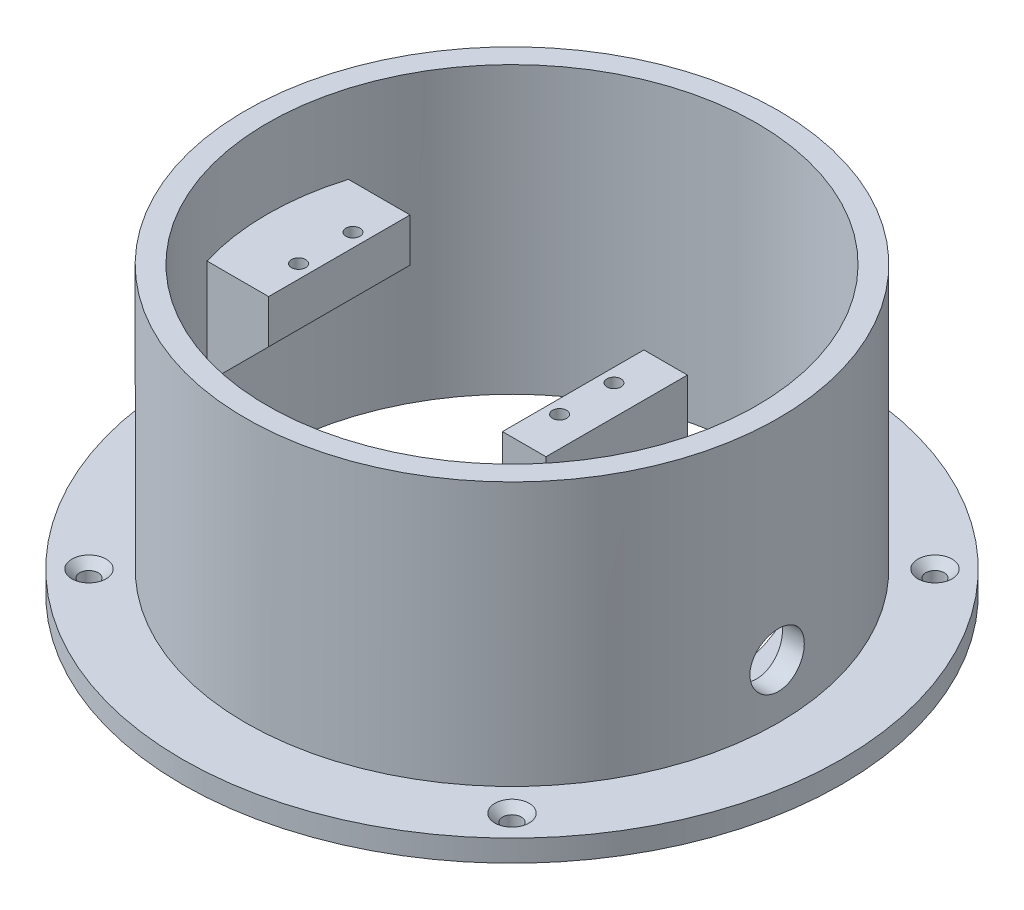
SolidWorks part; units mm, degrees
ref_plane "Front Plane" through (0, 0, 0) normal (0, 0, 1) x (1, 0, 0)
ref_plane "Top Plane" through (0, 0, 0) normal (0, 1, 0) x (1, 0, 0)
ref_plane "Right Plane" through (0, 0, 0) normal (1, 0, 0) x (0, 0, -1)
sketch "Sketch1" plane through (0, 0, 0) normal (0, 1, 0) x (1, 0, 0)
  circle A0 centre (0, 0) radius 60.625
  circle A1 centre (0, 0) radius 45
  dimension "D1" = 121.25
  dimension "D2" = 90
extrude "Boss-Extrude1" add sketch "Sketch1" along normal blind 4 contours A0
sketch "Sketch2" plane through (0, 4, 0) normal (0, 1, 0) x (1, 0, 0)
  circle A0 centre (0, 0) radius 45 construction
  circle A1 centre (0, 0) radius 45
  circle A2 centre (0, 0) radius 49
  dimension "D1" = 4
extrude "Boss-Extrude2" add sketch "Sketch2" along normal blind 52
ref_plane "Plane1" through (0, 36, 0) normal (0, 1, 0) x (1, 0, 0)
sketch "Sketch4" plane through (0, 0, 0) normal (0, 0, 1) x (1, 0, 0)
  line L0 (-60.625, 0) -> (60.625, 0) construction
  line L1 (11.25, 38) -> (19.25, 38)
  line L2 (11.25, 38) -> (11.25, 0)
  line L3 (11.25, 0) -> (19.25, 0)
  line L4 (19.25, 38) -> (19.25, 0)
  line L5 (49, 56) -> (-49, 56) construction
  line L6 (-45, 56) -> (-45, 4)
  line L7 (-31.75, 38) -> (-46.75, 38)
  line L8 (-31.75, 38) -> (-31.75, 30)
  line L9 (-31.75, 30) -> (-46.75, 30)
  line L10 (-46.75, 38) -> (-46.75, 30)
  line L11 (60.625, 4) -> (-60.625, 4) construction
  line L12 (-31.75, 30) -> (-45, 16.75)
  dimension "D1" = 11.25
  dimension "D2" = 8
  dimension "D3" = 18
  dimension "D4" = 43
  dimension "D5" = 15
  dimension "D6" = 8
  dimension "D7" = 45
  dimension "D8" = 18
extrude "Boss-Extrude4" add sketch "Sketch4" along normal mid plane 26 contours L9 L8 L7 L6 | L12 L9 L6 | L1 L4 L3 L2
sketch "Sketch5" plane through (0, 0, 0) normal (0, -1, 0) x (1, 0, 0)
  line L0 (11.25, 13) -> (29.0674, 34.3524)
  line L1 (11.25, -13) -> (29.0674, -34.3524)
  line L2 (11.25, 13) -> (11.25, -13)
  circle A0 centre (0, 0) radius 45 construction
  arc A1 (29.0674, -34.3524) -> (29.0674, 34.3524) centre (0, 0) ccw
extrude "Boss-Extrude5" add sketch "Sketch5" against normal up to surface (4 mm away) contours L0 A1 L1 L2 up to face at (0, 4, 60.625)
sketch "Sketch7" plane through (0, 38, 0) normal (0, 1, 0) x (1, 0, 0)
  line L0 (-31.75, -13) -> (-31.75, 13) construction
  circle A0 centre (-34.25, 5) radius 1.3
  circle A1 centre (-34.25, -5) radius 1.3
  circle A2 centre (13.75, 5) radius 1.3
  circle A3 centre (13.75, -5) radius 1.3
  dimension "D1" = 2.6
  dimension "D2" = 2.6
  dimension "D3" = 10
  dimension "D4" = 5
  dimension "D5" = 2.5
  dimension "D7" = 48
  dimension "D6" = 2
extrude "Cut-Extrude4" cut sketch "Sketch7" against normal blind 7.2
sketch "Sketch9" plane through (11.25, 0, 0) normal (-1, 0, 0) x (0, 0, 1)
  line L0 (13, 0) -> (-13, 0) construction
  line L1 (-5, 29) -> (5, 29)
  line L2 (-5, 29) -> (-5, 0)
  line L3 (-5, 0) -> (5, 0)
  line L4 (5, 29) -> (5, 0)
  line L5 (-5, 29) -> (5, 0) construction
  line L6 (-5, 0) -> (5, 29) construction
  line L7 (0, 0) -> (0, 29) construction
  line L8 (13, 38) -> (-13, 38) construction
  line L10 (5, 5) -> (-5, 5)
  point P0 (0, 14.5)
  dimension "D1" = 10
  dimension "D2" = 9
  dimension "D3" = 5
extrude "Cut-Extrude7" cut sketch "Sketch9" against normal up to surface (8 mm away) contours L10 L4 L1 L2 up to face at (19.25, 21, 0)
ref_plane "Plane2" through (49, 0, 0) normal (1, 0, 0) x (0, 0, -1)
sketch "Sketch11" plane through (49, 0, 0) normal (1, 0, 0) x (0, 0, -1)
  circle A0 centre (0, 14) radius 5
  dimension "D1" = 10
  dimension "D2" = 14
extrude "Cut-Extrude8" cut sketch "Sketch11" against normal up to next
sketch "Sketch12" plane through (0, 4, 0) normal (0, 1, 0) x (1, 0, 0)
  line L5 (27.25, 19.6878) -> (27.25, -19.6878)
  line L6 (27.25, 19.6878) -> (27.25, -19.6878)
  line L9 (24.25, 16.0926) -> (24.25, -16.0926)
  line L10 (19.25, -13) -> (19.25, 13) construction
  line L18 (27.25, -19.6878) -> (29.4795, -22.3597)
  line L19 (29.4795, 22.3597) -> (27.25, 19.6878)
  line L21 (24.25, -16.0926) -> (29.4795, -22.3597)
  line L22 (29.4795, 22.3597) -> (24.25, 16.0926)
  arc A2 (29.4795, -22.3597) -> (29.4795, 22.3597) centre (0, 0) ccw
  arc A3 (29.4795, -22.3597) -> (29.4795, 22.3597) centre (0, 0) ccw
  dimension "D2" = 5
  dimension "D1" = 8
extrude "Cut-Extrude9" cut sketch "Sketch12" against normal through all contours L21 A3 L22 L6 | L6 L22 L9 L21
sketch "Sketch14" plane through (0, 4, 0) normal (0, 1, 0) x (1, 0, 0)
  line L0 (0, 0) -> (-38.8909, 38.8909) construction
  line L1 (11.25, 13) -> (19.25, 13) construction
  circle A0 centre (-38.8909, 38.8909) radius 1.5
  circle A1 centre (38.8909, 38.8909) radius 1.5
  circle A2 centre (38.8909, -38.8909) radius 1.5
  circle A3 centre (-38.8909, -38.8909) radius 1.5
  point P15 (0, 0)
  dimension "D1" = 3
  dimension "D2" = 55
  dimension "D3" = 135
  dimension "D4" = 4
hole_wizard "CSK for M3 Countersunk Flat Head Screw1" positions "Sketch15" profile "Sketch17" countersink size "M3" standard "DIN" end condition up to next
sketch "Sketch15" plane through (0, 4, 0) normal (0, 1, 0) x (1, 0, 0)
  point P0 (-38.8909, 38.8909)
  point P3 (-38.8909, -38.8909)
  point P6 (38.8909, -38.8909)
  point P9 (38.8909, 38.8909)
sketch "Sketch17" plane through (-38.8909, 4, -38.8909) normal (1, 0, 0) x (0, 0, 1)
  line L0 (0, 0) -> (0, 4)
  line L1 (0, 4) -> (1.7, 4)
  line L2 (1.7, 4) -> (1.7, 1.45)
  line L3 (1.7, 1.45) -> (3.15, 0)
  line L5 (3.15, 0) -> (0, 0)
  line L6 (-1.7, 1.45) -> (-3.15, 0) construction
  line L11 (0, -6.35) -> (0, 107.95) construction
  dimension "Thru Hole Dia." = 3.4
  dimension "Thru Hole Depth" = 4
  dimension "Near C'Sink Dia." = 6.3
  dimension "Near C'Sink Angle" = 90
sketch "Sketch18" plane through (0, 0, 0) normal (0, 0, 1) x (1, 0, 0)
  line L0 (45, 56) -> (-45, 56) construction
  line L1 (-49, 59.5) -> (49, 59.5)
  line L2 (-49, 59.5) -> (-49, 52.5)
  line L3 (-49, 52.5) -> (49, 52.5)
  line L4 (49, 59.5) -> (49, 52.5)
  line L5 (-49, 59.5) -> (49, 52.5) construction
  line L6 (-49, 52.5) -> (49, 59.5) construction
  line L7 (49, 18.9999) -> (49, 56) construction
  point P0 (0, 56)
  dimension "D1" = 7
extrude "Cut-Extrude10" cut sketch "Sketch18" against normal through all both and the other way through all
